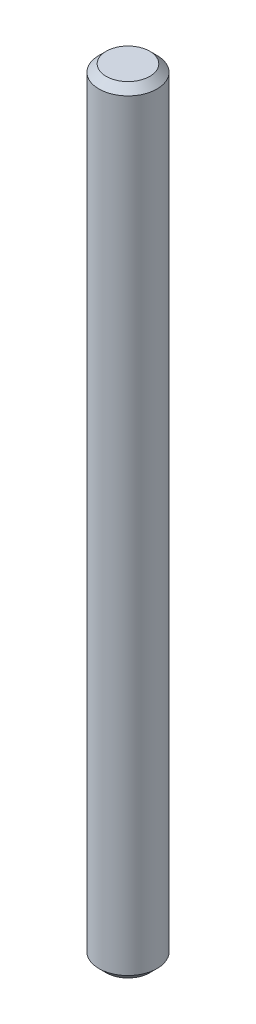
SolidWorks part; units mm, degrees
material "6063-T5"
ref_plane "Front Plane" through (0, 0, 0) normal (0, 0, 1) x (1, 0, 0)
ref_plane "Top Plane" through (0, 0, 0) normal (0, 1, 0) x (1, 0, 0)
ref_plane "Right Plane" through (0, 0, 0) normal (1, 0, 0) x (0, 0, -1)
ref_plane "Plane1" through (0, 0, 0) normal (0, 0, 1) x (1, 0, 0)
sketch "Sketch1" plane through (0, 0, 0) normal (0, 0, 1) x (1, 0, 0)
  line L0 (0, 26.7) -> (1.5, 26.7)
  line L1 (1.5, 26.7) -> (2, 26.2)
  line L2 (2, 26.2) -> (2, -26.2)
  line L3 (2, -26.2) -> (1.5, -26.7)
  line L4 (1.5, -26.7) -> (0, -26.7)
  line L5 (0, -26.7) -> (0, 26.7)
  line L6 (0, -26.7) -> (0, 26.7) construction
revolve "Revolve1" add sketch "Sketch1" angle 360 about L6
